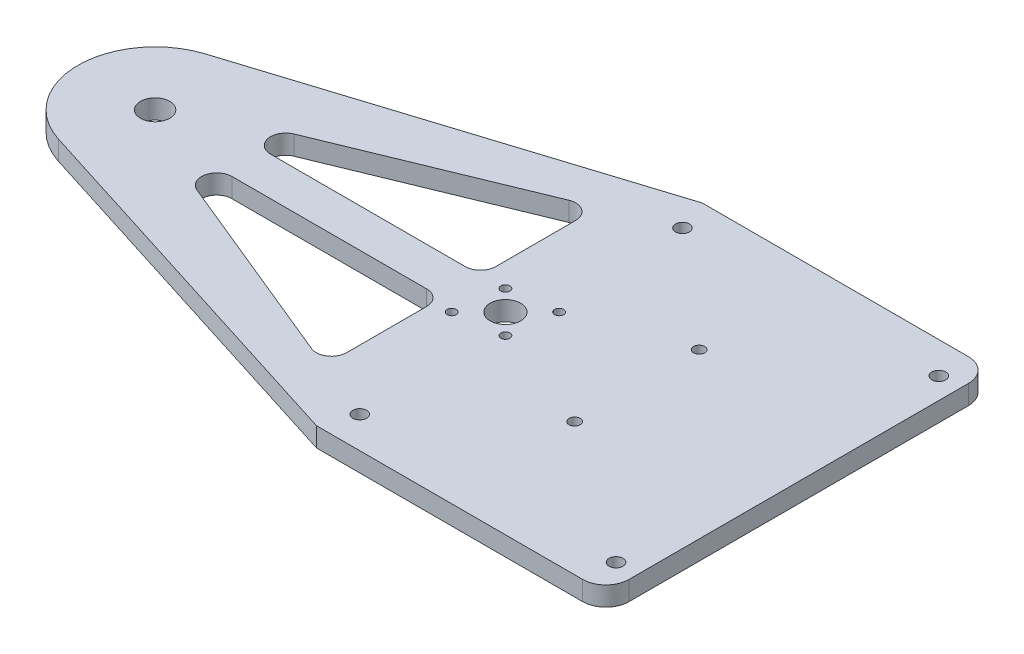
SolidWorks part; units mm, degrees
material "UHMW"
ref_plane "Front Plane" through (0, 0, 0) normal (0, 0, 1) x (1, 0, 0)
ref_plane "Top Plane" through (0, 0, 0) normal (0, 1, 0) x (1, 0, 0)
ref_plane "Right Plane" through (0, 0, 0) normal (1, 0, 0) x (0, 0, -1)
sketch "Sketch1" plane through (0, 0, 0) normal (0, 1, 0) x (1, 0, 0)
  line L0 (-47.625, 0) -> (47.625, 0) construction
  line L1 (-47.625, -63.5) -> (47.625, -63.5)
  line L2 (-47.625, -63.5) -> (-47.625, 63.5)
  line L3 (-47.625, 63.5) -> (47.625, 63.5)
  line L4 (47.625, -63.5) -> (47.625, 63.5)
  line L5 (-47.625, -63.5) -> (47.625, 63.5) construction
  line L6 (-47.625, 63.5) -> (47.625, -63.5) construction
  point P0 (0, 0)
  dimension "D1" = 95.25
  dimension "D2" = 127
  dimension "D3" = 63.5
extrude "Boss-Extrude1" add sketch "Sketch1" along normal blind 6.35
sketch "Sketch4" plane through (0, 6.35, 0) normal (0, 1, 0) x (1, 0, 0)
  line L1 (-47.625, 63.5) -> (-171.916, 24.2193)
  line L5 (-47.625, 63.5) -> (-47.625, -63.5) construction
  line L9 (-47.625, -63.5) -> (-171.916, -24.2193)
  line L10 (-47.625, 63.5) -> (-47.625, -63.5)
  arc A0 (-171.916, 24.2193) -> (-171.916, -24.2193) centre (-164.2618, 0) ccw
  circle A1 centre (-48.9458, 0) radius 2.5 construction
  dimension "D1" = 50.8
  dimension "D2" = 115.316
extrude "Boss-Extrude3" add sketch "Sketch4" against normal blind 6.35
sketch "Sketch5" plane through (0, 6.35, 0) normal (0, 1, 0) x (1, 0, 0)
  line L0 (-48.9458, 0) -> (-31.7264, 0) construction
  line L3 (-48.9458, 0) -> (-91.3931, 0) construction
  circle A0 centre (-164.2618, 0) radius 4.826
  circle A1 centre (-48.9458, 0) radius 5.04
  arc A2 (-171.916, 24.2193) -> (-171.916, -24.2193) centre (-164.2618, 0) ccw construction
  arc A3 (-171.916, 24.2193) -> (-171.916, -24.2193) centre (-164.2618, 0) ccw
  circle A4 centre (-42.2283, -6.7175) radius 1.5
  circle A5 centre (-40.107, 8.8388) radius 1.5
  circle A6 centre (-57.7846, -8.8388) radius 1.5
  circle A7 centre (-55.6633, 6.7175) radius 1.5
  circle A8 centre (-40.107, 8.8388) radius 1.5 construction
  circle A9 centre (-55.6633, 6.7175) radius 1.5 construction
  circle A10 centre (-57.7846, -8.8388) radius 1.5 construction
  circle A11 centre (-42.2283, -6.7175) radius 1.5 construction
  point P17 (0, 0)
  point P20 (-48.9458, 0)
  point P31 (0.5322, 0.0741)
  dimension "D1" = 9.652
  dimension "D2" = 17.2194
  dimension "D4" = 48.9458
  dimension "D3" = 10.08
extrude "Cut-Extrude1" cut sketch "Sketch5" against normal through all contours A0 | A1 | A5 | A6 | A7 | A4
sketch "Sketch6" plane through (0, 6.35, 0) normal (0, 1, 0) x (1, 0, 0)
  line L0 (-63.5, 6.35) -> (-63.5, -6.35) construction
  line L1 (-63.5, 45.1637) -> (-157.9118, 6.35)
  line L2 (-157.9118, 6.35) -> (-63.5, 6.35)
  line L3 (-63.5, 6.35) -> (-63.5, 45.1637)
  line L4 (-63.5, -6.35) -> (-63.5, -45.1637)
  line L5 (-63.5, -45.1637) -> (-157.9118, -6.35)
  line L6 (-157.9118, -6.35) -> (-63.5, -6.35)
  line L7 (0, 0) -> (-63.5, 0) construction
  line L8 (-189.6618, 75.5498) -> (-189.6618, -75.5498) construction
  line L9 (-47.625, 63.5) -> (-171.916, 24.2193) construction
  arc A0 (-171.916, 24.2193) -> (-171.916, -24.2193) centre (-164.2618, 0) ccw construction
  point P12 (-189.6618, 0)
  dimension "D1" = 31.75
  dimension "D2" = 12.7
  dimension "D3" = 12.7
  dimension "D4" = 63.5
extrude "Cut-Extrude2" cut sketch "Sketch6" against normal through all
fillet "Fillet9" radius 5 6 edges at (-157.9118, 3.175, 6.35) (-63.5, 3.175, 6.35) (-63.5, 3.175, 45.1637) (-63.5, 3.175, -6.35) (-157.9118, 3.175, -6.35) (-63.5, 3.175, -45.1637)
fillet "Fillet10" radius 7.62 2 edges at (47.625, 3.175, -63.5) (47.625, 3.175, 63.5)
sketch "Sketch7" plane through (0, 6.35, 0) normal (0, 1, 0) x (1, 0, 0)
  circle A0 centre (-43.7773, -53.1254) radius 2.2812
  circle A1 centre (-43.7773, 53.1254) radius 2.2812
  circle A2 centre (40.6023, 53.1254) radius 2.2812
  circle A3 centre (40.6023, -53.1254) radius 2.2812
  circle A4 centre (-43.7773, 53.1254) radius 2.2812 construction
  circle A5 centre (40.6023, 53.1254) radius 2.2812 construction
  circle A6 centre (40.6023, -53.1254) radius 2.2812 construction
  circle A7 centre (-43.7773, -53.1254) radius 2.2812 construction
extrude "Cut-Extrude3" cut sketch "Sketch7" against normal through all
sketch "Sketch8" plane through (0, 6.35, 0) normal (0, 1, 0) x (1, 0, 0)
  circle A0 centre (-6.3285, -19.8289) radius 1.83
  circle A1 centre (-6.3283, 21.1715) radius 1.83
  circle A2 centre (-6.3285, -19.8289) radius 1.83 construction
  circle A3 centre (-6.3283, 21.1715) radius 1.83 construction
extrude "Cut-Extrude4" cut sketch "Sketch8" against normal through all
